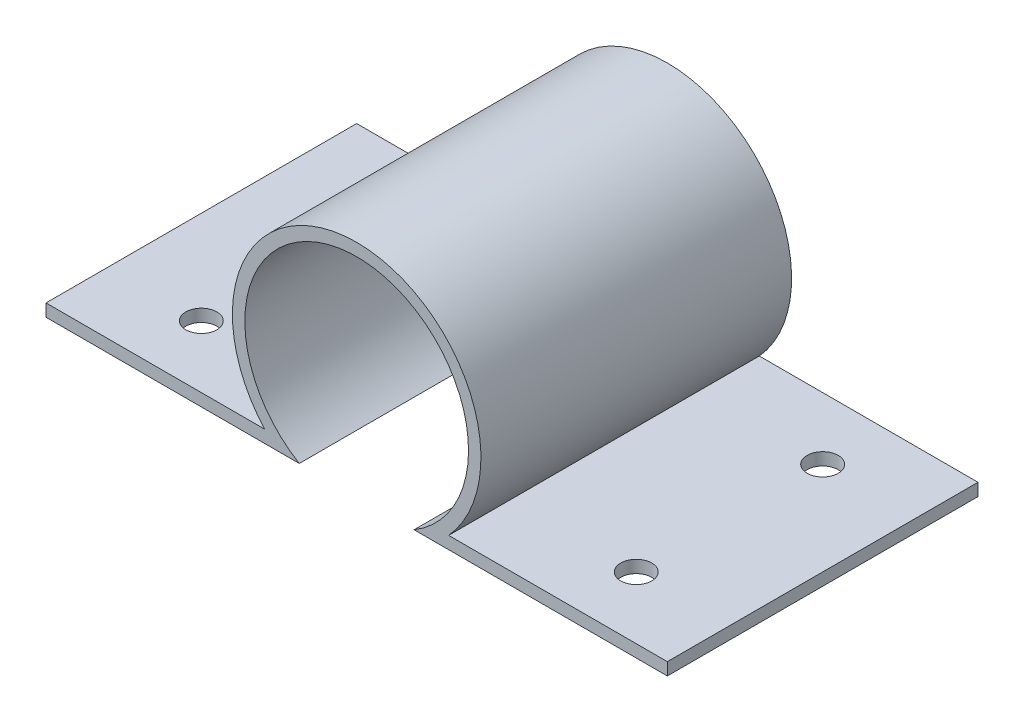
SolidWorks part; units mm, degrees
ref_plane "Front Plane" through (0, 0, 0) normal (0, 0, 1) x (1, 0, 0)
ref_plane "Top Plane" through (0, 0, 0) normal (0, 1, 0) x (1, 0, 0)
ref_plane "Right Plane" through (0, 0, 0) normal (1, 0, 0) x (0, 0, -1)
sketch "Sketch1" plane through (0, 0, 0) normal (0, 0, 1) x (1, 0, 0)
  line L0 (-50, 0) -> (-14.8033, 0)
  line L1 (14.8033, 0) -> (50, 0)
  line L2 (-50, -2) -> (-9.2383, -2)
  line L3 (9.2383, -2) -> (50, -2)
  line L4 (-50, 0) -> (-50, -2)
  line L5 (50, 0) -> (50, -2)
  arc A0 (14.8033, 0) -> (-14.8033, 0) centre (0, 13.4485) ccw
  arc A1 (9.2383, -2) -> (-9.2383, -2) centre (0, 13.4485) ccw
  dimension "D2" = 20
  dimension "D1" = 100
extrude "Boss-Extrude2" add sketch "Sketch1" along normal blind 50
sketch "Sketch3" plane through (0, 0, 0) normal (0, 1, 0) x (1, 0, 0)
  line L0 (50, -25) -> (-50, -25) construction
  line L1 (50, -50) -> (50, 0) construction
  line L2 (-50, -50) -> (-50, 0) construction
  line L3 (0, -25) -> (0, -5.9204) construction
  circle A0 centre (35, -10) radius 2.5
  circle A1 centre (35, -40) radius 2.5
  circle A2 centre (-35, -40) radius 2.5
  circle A3 centre (-35, -10) radius 2.5
  dimension "D1" = 5
  dimension "D2" = 30
  dimension "D3" = 70
extrude "Cut-Extrude2" cut sketch "Sketch3" against normal blind 50
